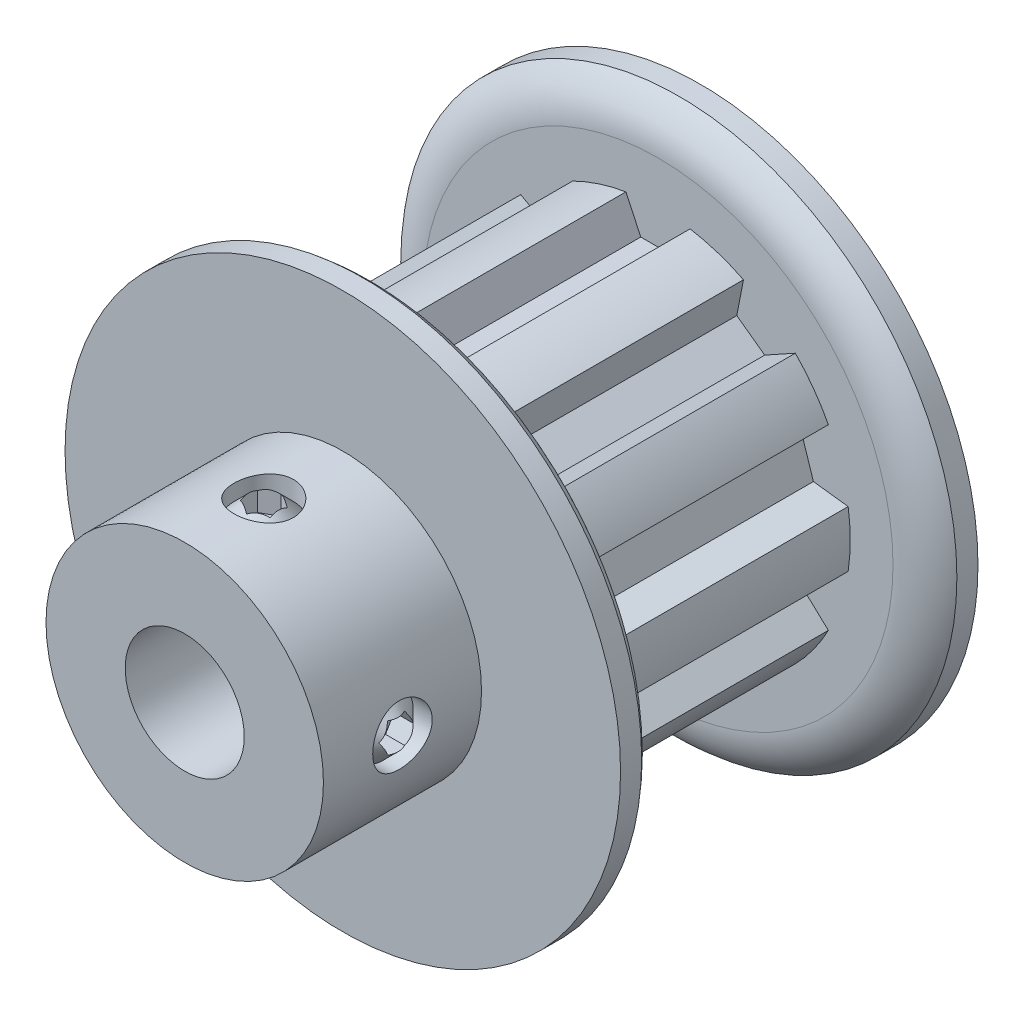
SolidWorks part; units mm, degrees
ref_plane "Front Plane" through (0, 0, 0) normal (0, 0, 1) x (1, 0, 0)
ref_plane "Top Plane" through (0, 0, 0) normal (0, 1, 0) x (1, 0, 0)
ref_plane "Right Plane" through (0, 0, 0) normal (1, 0, 0) x (0, 0, -1)
sketch "Sketch1" plane through (0, 0, 0) normal (0, 0, 1) x (1, 0, 0)
  line L0 (-1.2827, 7.5819) -> (-0.6905, 6.3119)
  line L1 (-0.6905, 6.3119) -> (0.6905, 6.3119)
  line L2 (0.6905, 6.3119) -> (1.2827, 7.5819)
  line L3 (-1.2827, 7.5819) -> (1.2827, 7.5819)
  line L4 (0, 0) -> (0, 6.3119) construction
  line L5 (0, 6.3119) -> (0, 8.5979) construction
  circle A0 centre (0, 0) radius 8.0899 construction
  circle A1 centre (0, 0) radius 11.1125 construction
  circle A2 centre (0, 0) radius 7.6896 construction
  point P6 (0, 7.5819)
  point P11 (0, 8.0899)
  point P13 (0, 11.1125)
  point P14 (0, 7.6896)
  dimension "D2" = 0.508
sketch "Sketch2" plane through (0, 0, 0) normal (1, 0, 0) x (0, 0, -1)
  line L0 (-10.3124, 2.3812) -> (10.3124, 2.3812)
  line L1 (-10.3124, 2.3812) -> (-10.3124, 5.5499)
  line L2 (-10.3124, 5.5499) -> (-3.9878, 5.5499)
  line L3 (-3.9878, 5.5499) -> (-3.9878, 11.1125)
  line L4 (-3.9878, 11.1125) -> (-2.2987, 11.1125) construction
  line L5 (-2.2987, 11.1125) -> (-2.2987, 7.6896) construction
  line L6 (-2.2987, 7.6896) -> (8.6233, 7.6896)
  line L7 (8.6233, 7.6896) -> (8.6233, 11.1125) construction
  line L8 (8.6233, 11.1125) -> (10.3124, 11.1125) construction
  line L9 (10.3124, 11.1125) -> (10.3124, 2.3812)
  line L10 (-10.3124, 0) -> (10.3124, 0) construction
  line L13 (-3.9878, 11.1125) -> (-3.1432, 11.1125)
  line L14 (-2.2987, 9.4011) -> (-2.2987, 7.6896)
  line L15 (8.6233, 7.6896) -> (8.6233, 9.4011)
  line L16 (9.4679, 11.1125) -> (10.3124, 11.1125)
  arc A0 (-2.2987, 9.4011) -> (-3.1432, 11.1125) centre (-4.455, 9.4011) ccw
  arc A1 (8.6233, 9.4011) -> (9.4679, 11.1125) centre (10.7796, 9.4011) cw
  point P12 (-2.2987, 9.4011)
  point P14 (-3.1432, 11.1125)
  point P20 (8.6233, 9.4011)
  point P21 (9.4679, 11.1125)
  point P25 (8.6233, 0)
  point P26 (-2.2987, 0)
  dimension "Bore" = 4.7625
  dimension "Hub Dia" = 11.0998
  dimension "Outside Width" = 14.3002
  dimension "Inside Width" = 10.922
revolve "Revolve1" add sketch "Sketch2" angle 360 mid plane about L10
sketch "Sketch3" plane through (0, 0, 0) normal (0, 0, 1) x (1, 0, 0)
  line L0 (-0.6905, 6.3119) -> (0.6905, 6.3119) construction
  line L1 (0.6905, 6.3119) -> (1.2827, 7.5819) construction
  line L2 (-1.2827, 7.5819) -> (-0.6905, 6.3119) construction
  line L3 (-0.6905, 6.3119) -> (0.6905, 6.3119)
  line L4 (0.6905, 6.3119) -> (1.2827, 7.5819)
  line L5 (-1.2827, 7.5819) -> (-0.6905, 6.3119)
  circle A0 centre (0, 0) radius 7.6896 construction
  arc A1 (1.2827, 7.5819) -> (-1.2827, 7.5819) centre (0, 0) ccw
extrude "Cut-Extrude1" cut sketch "Sketch3" against normal up to vertex (8.6233 mm away) from vertex at 2.2987 starting at point (0, 7.6896, 2.2987)
pattern_circular "CirPattern1" count 10 over 360 about axis through (0, 0, 0) along (0, 0, 1) of "Cut-Extrude1"
sketch "Sketch4" plane through (0, 0, 0) normal (0, 1, 0) x (1, 0, 0)
  line L0 (0, -3.9878) -> (0, -10.3124) construction
  line L1 (-5.5499, -3.9878) -> (5.5499, -3.9878) construction
  line L2 (-5.5499, -10.3124) -> (5.5499, -10.3124) construction
  circle A0 centre (0, -7.1501) radius 1.1906
  dimension "D1" = 2.3813
extrude "Cut-Extrude2" cut sketch "Sketch4" along normal through all
ref_plane "Plane1" through (0, 0, 7.1501) normal (0, 0, 1) x (1, 0, 0)
sketch "Sketch5" plane through (0, 0, 7.1501) normal (0, 0, 1) x (1, 0, 0)
  line L0 (0, 0) -> (0, 5.5499) construction
  line L1 (-1.1906, 5.4207) -> (-1.1906, 2.0622) construction
  line L2 (-1.1906, 5.4207) -> (-1.1906, 2.0622) construction
  line L3 (0, 5.4207) -> (0, 2.3812)
  line L4 (0, 2.3812) -> (-0.5556, 2.3812)
  line L5 (-1.1906, 4.7857) -> (-1.1906, 3.0162)
  line L6 (-0.5556, 5.4207) -> (0, 5.4207)
  line L7 (-1.1906, 4.7857) -> (-0.5556, 5.4207)
  line L8 (-1.1906, 3.0162) -> (-0.5556, 2.3812)
  circle A0 centre (0, 0) radius 5.5499 construction
  circle A3 centre (0, 0) radius 2.3812 construction
  point P13 (-1.1906, 2.3812)
  point P15 (-1.1906, 5.4207)
revolve "Revolve2" add sketch "Sketch5" angle 360 mid plane about L0
sketch "Sketch6" plane through (0, 5.4207, 0) normal (0, -1, 0) x (-1, 0, 0)
  line L1 (0, -6.4627) -> (-0.5953, -6.8064)
  line L2 (-0.5953, -6.8064) -> (-0.5953, -7.4938)
  line L3 (-0.5953, -7.4938) -> (0, -7.8375)
  line L4 (0, -7.8375) -> (0.5953, -7.4938)
  line L5 (0.5953, -7.4938) -> (0.5953, -6.8064)
  line L6 (0.5953, -6.8064) -> (0, -6.4627)
  circle A0 centre (0, -7.1501) radius 0.5953 construction
  dimension "D1" = 1.1906
extrude "Cut-Extrude3" cut sketch "Sketch6" along normal blind 0.893
pattern_circular "CirPattern2" count 2 every 90 about axis through (0, 0, 0) along (0, 0, 1) of "Cut-Extrude2", "Revolve2", "Cut-Extrude3"
equation "\"D2@Sketch1\" = \"D1@Sketch1\"/2"
equation "\"D1@Sketch4\" = \"Bore@Sketch2\"/2"
equation "\"D1@Sketch6\" = \"D1@Sketch4\"/2"
equation "\"D1@Cut-Extrude3\" = \"D1@Sketch6\"*.75"
